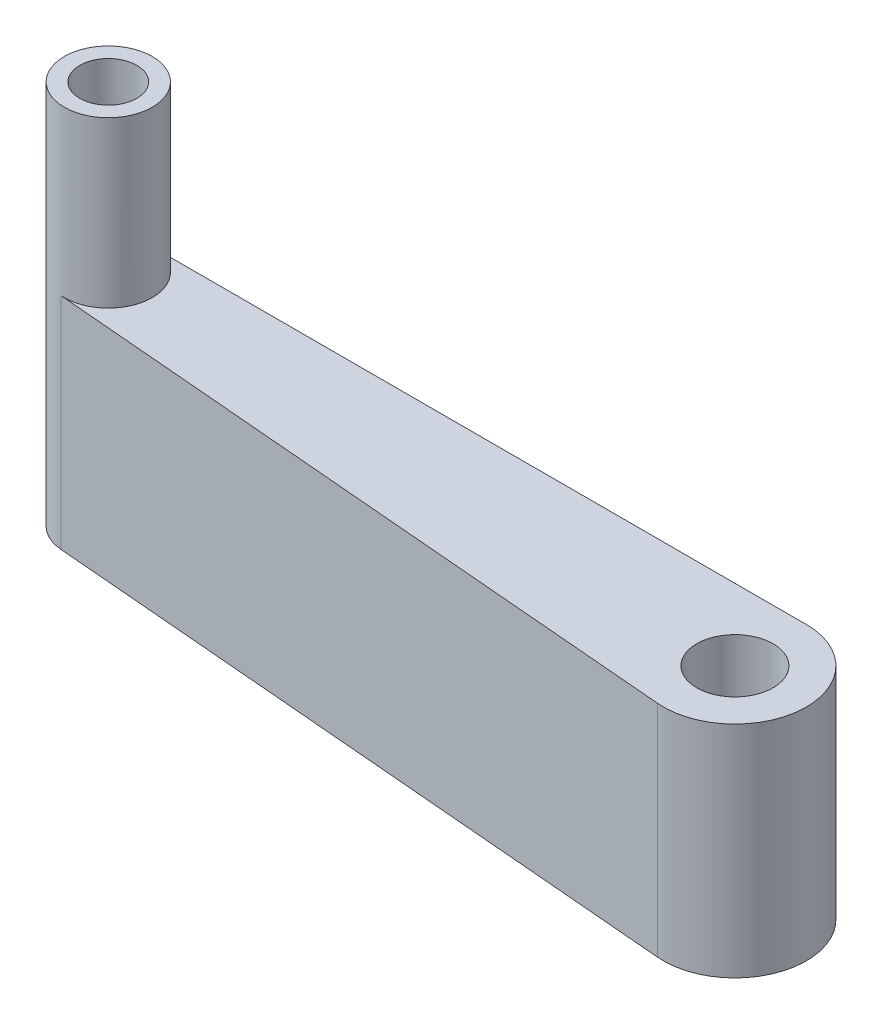
SolidWorks part; units mm, degrees
ref_plane "Alzado" through (0, 0, 0) normal (0, 0, 1) x (1, 0, 0)
ref_plane "Planta" through (0, 0, 0) normal (0, 1, 0) x (1, 0, 0)
ref_plane "Vista lateral" through (0, 0, 0) normal (1, 0, 0) x (0, 0, -1)
sketch "Croquis1" plane through (0, 0, 0) normal (0, 1, 0) x (1, 0, 0)
  line L0 (-59.5, 6.5) -> (0, 6.5)
  line L2 (0, 15.0922) -> (0, -13.2624) construction
  line L3 (70.9164, 0) -> (-21.8302, 0) construction
  line L4 (-59.8355, -1.4859) -> (-0.5453, -6.4771)
  arc A0 (-59.5, 6.5) -> (-59.8355, -1.4859) centre (-59.5, 2.5) ccw
  arc A2 (-0.5453, -6.4771) -> (0, 6.5) centre (0, 0) ccw
  point P6 (0, 0)
  dimension "D1" = 13
  dimension "D2" = 4
  dimension "D4" = 70
extrude "Saliente-Extruir1" add sketch "Croquis1" along normal mid plane 20
sketch "Croquis2" plane through (0, 10, 0) normal (0, 1, 0) x (1, 0, 0)
  circle A0 centre (0, 0) radius 3.475
  dimension "D1" = 6.95
extrude "Cortar-Extruir1" cut sketch "Croquis2" against normal through all
sketch "Croquis3" plane through (0, 10, 0) normal (0, 1, 0) x (1, 0, 0)
  circle A0 centre (-59.5, 2.5) radius 4
  arc A1 (-59.5, 6.5) -> (-59.8355, -1.4859) centre (-59.5, 2.5) ccw construction
extrude "Saliente-Extruir2" add sketch "Croquis3" along normal blind 15
sketch "Croquis4" plane through (0, 25, 0) normal (0, 1, 0) x (1, 0, 0)
  circle A0 centre (-59.5, 2.5) radius 2.6
  dimension "D1" = 5.2
extrude "Cortar-Extruir2" cut sketch "Croquis4" against normal blind 6 contours A0
